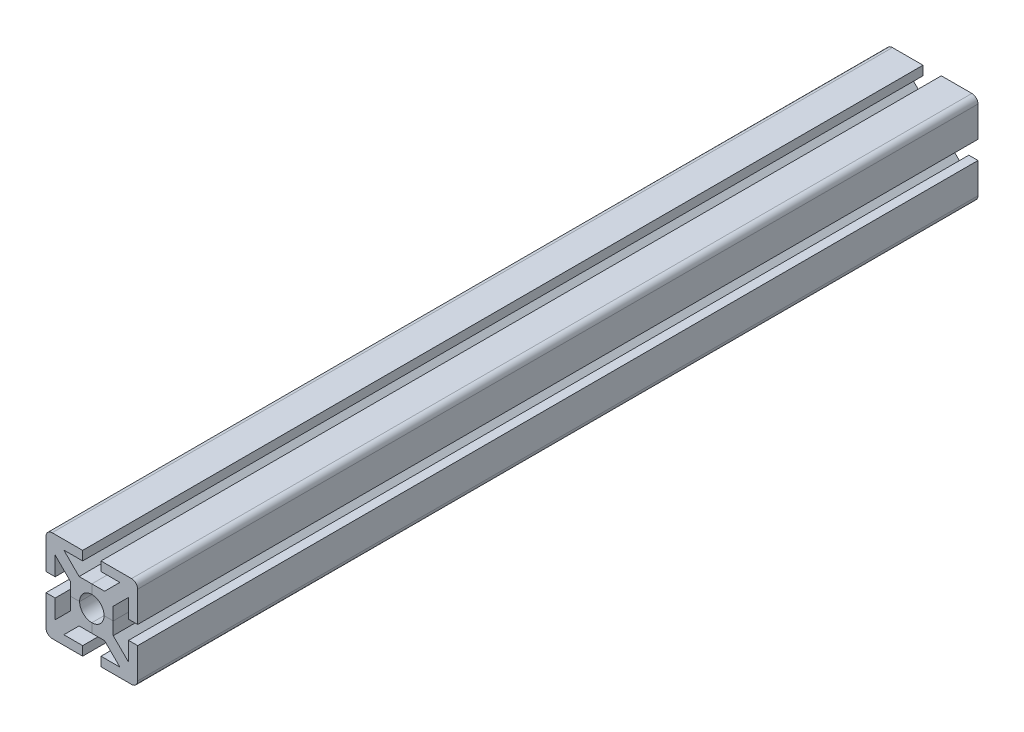
SolidWorks part; units mm, degrees
ref_plane "Alzado" through (0, 0, 0) normal (0, 0, 1) x (1, 0, 0)
ref_plane "Planta" through (0, 0, 0) normal (0, 1, 0) x (1, 0, 0)
ref_plane "Vista lateral" through (0, 0, 0) normal (1, 0, 0) x (0, 0, -1)
sketch "Croquis1" plane through (0, 0, 0) normal (0, 0, 1) x (1, 0, 0)
  line L0 (0, 0) -> (50000, 0) construction
  line L1 (-15, 15) -> (15, 15) construction
  line L2 (-15, 15) -> (-15, -15) construction
  line L3 (-15, -15) -> (15, -15) construction
  line L4 (15, 15) -> (15, -15) construction
  line L5 (-15, 15) -> (15, -15) construction
  line L6 (-15, -15) -> (15, 15) construction
  line L7 (0, 0) -> (0, -50000) construction
  line L8 (0, 4) -> (0, 7)
  line L9 (0, 7) -> (4.1716, 7)
  line L10 (4.1716, 7) -> (9.1716, 12)
  line L11 (9.1716, 12) -> (3, 12)
  line L12 (3, 12) -> (3, 15)
  line L13 (3, 15) -> (15, 15)
  line L20 (2.8284, 2.8284) -> (15, 15)
  arc A0 (2.8284, 2.8284) -> (0, 4) centre (0, 0) ccw
  point P0 (0, 0)
  dimension "D3" = 4
  dimension "D1" = 30
  dimension "D2" = 6
  dimension "D4" = 8
  dimension "D5" = 3
  dimension "D6" = 2
extrude "Saliente-Extruir1" add sketch "Croquis1" along normal mid plane 275
mirror "Simetría1" about plane through (2.8284, 2.8284, 137.5) normal (-0.7071, 0.7071, 0) of "Saliente-Extruir1"
fillet "Redondeo1" radius 2 1 edges at (15, 15, 0)
pattern_circular "MatrizC4" count 4 over 360 about axis through (0, 0, 0) along (0, 0, 1) of bodies 102
